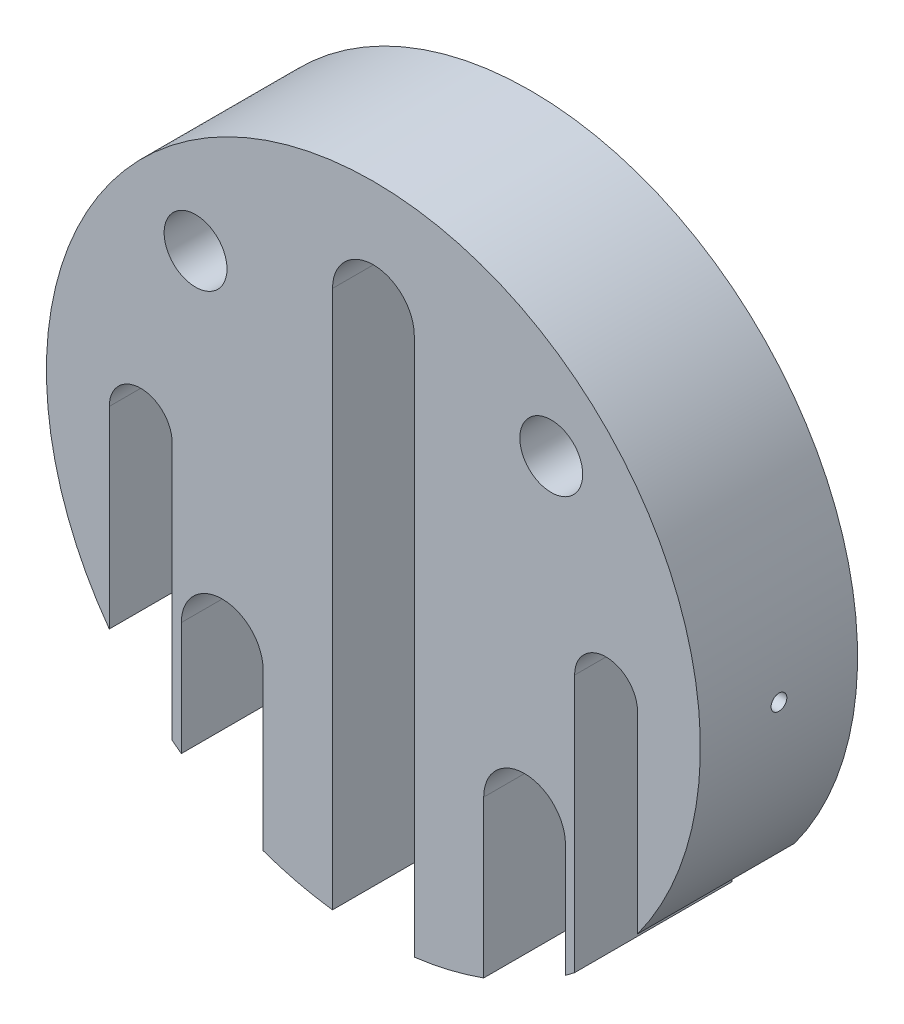
SolidWorks part; units mm, degrees
material "Malleable Cast Iron"
ref_plane "Front Plane" through (0, 0, 0) normal (0, 0, 1) x (1, 0, 0)
ref_plane "Top Plane" through (0, 0, 0) normal (0, 1, 0) x (1, 0, 0)
ref_plane "Right Plane" through (0, 0, 0) normal (1, 0, 0) x (0, 0, -1)
sketch "Sketch1" plane through (0, 0, 0) normal (0, 0, 1) x (1, 0, 0)
  circle A0 centre (0, 0) radius 52
  dimension "D1" = 104
extrude "Boss-Extrude1" add sketch "Sketch1" along normal blind 25
sketch "Sketch2" plane through (0, 0, 25) normal (0, 0, 1) x (1, 0, 0)
  line L0 (0, 0) -> (0, -16.5156) construction
  line L2 (32, 0) -> (32, -45)
  line L3 (32, -45) -> (42, -45)
  line L4 (42, 0) -> (42, -45)
  line L6 (-5, -40) -> (-5, -55)
  line L7 (-5, -55) -> (5, -55)
  line L8 (5, -40) -> (5, -55)
  line L9 (-32, -45) -> (-42, -45)
  line L10 (-42, 0) -> (-42, -45)
  line L12 (-32, 0) -> (-32, -45)
  arc A1 (32, 0) -> (42, 0) centre (37, 0) cw
  arc A2 (-32, 0) -> (-42, 0) centre (-37, 0) ccw
  arc A3 (5, -40) -> (-5, -40) centre (0, -40) ccw
  dimension "D9" = 5
  dimension "D3" = 5
  dimension "D2" = 5
extrude "Cut-Extrude1" cut sketch "Sketch2" against normal blind 25
sketch "Sketch3" plane through (0, 0, 25) normal (0, 0, 1) x (1, 0, 0)
  circle A0 centre (0, 34) radius 6.5
  dimension "D1" = 13
  dimension "D2" = 34
extrude "Cut-Extrude2" cut sketch "Sketch3" against normal blind 30 contours A0
sketch "Sketch5" plane through (0, 0, 25) normal (0, 0, 1) x (1, 0, 0)
  line L0 (0, 0) -> (-24.0416, -24.0416) construction
  line L1 (0, 0) -> (0, -28.0674) construction
  circle A0 centre (-24.0416, -24.0416) radius 6.5
  dimension "D1" = 13
  dimension "D2" = 34
  dimension "D3" = 45
extrude "Cut-Extrude3" cut sketch "Sketch5" against normal blind 30
mirror "Mirror1" about plane through (0, 0, 0) normal (1, 0, 0) of "Cut-Extrude3"
sketch "Sketch6" plane through (0, 0, 25) normal (0, 0, 1) x (1, 0, 0)
  line L0 (-6.5, 34) -> (6.5, 34)
  line L1 (-6.5, 34) -> (-6.5, -56.1062)
  line L2 (6.5, 34) -> (6.5, -56.1062)
  line L3 (-6.5, -56.1062) -> (6.5, -56.1062)
  line L4 (17.5416, -24.0416) -> (30.5416, -24.0416)
  line L5 (17.5416, -24.0416) -> (17.5416, -50.2523)
  line L6 (30.5416, -24.0416) -> (30.5416, -50.2523)
  line L7 (17.5416, -50.2523) -> (30.5416, -50.2523)
  line L8 (-30.5416, -24.0416) -> (-17.5416, -24.0416)
  line L9 (-30.5416, -24.0416) -> (-30.5416, -53.8028)
  line L10 (-17.5416, -24.0416) -> (-17.5416, -53.8028)
  line L11 (-30.5416, -53.8028) -> (-17.5416, -53.8028)
  circle A0 centre (0, 34) radius 6.5 construction
  circle A1 centre (24.0416, -24.0416) radius 6.5 construction
  circle A2 centre (-24.0416, -24.0416) radius 6.5 construction
extrude "Cut-Extrude4" cut sketch "Sketch6" against normal blind 30
ref_plane "Plane1" through (-52, 0, 0) normal (-1, 0, 0) x (0, 0, 1)
hole_wizard "M3 Tapped Hole1" positions "Sketch8" profile "Sketch9" tap size "M3" standard "ISO"
sketch "Sketch8" plane through (-52, 0, 0) normal (-1, 0, 0) x (0, 0, 1)
  line L0 (0, 52) -> (0, -30.6594) construction
  point P0 (12.5, 0)
  dimension "D1" = 12.5
sketch "Sketch9" plane through (-52, 0, 12.5) normal (0, 1, 0) x (0, 0, 1)
  line L0 (0, 0) -> (0, 45.5)
  line L1 (0, 45.5) -> (1.25, 45.5)
  line L2 (1.25, 45.5) -> (1.25, 0)
  line L5 (1.25, 0) -> (0, 0)
  line L11 (0, -6.35) -> (0, 107.95) construction
  dimension "Thru Tap Drill Dia." = 2.5
  dimension "Thru Tap Drill Depth" = 45.5
cosmetic thread "Hole Thread2" parameters "D2"=3
mirror "Mirror2" about plane through (0, 0, 0) normal (1, 0, 0) of "M3 Tapped Hole1"
sketch "Sketch10" plane through (0, 0, 25) normal (0, 0, 1) x (1, 0, 0)
  line L0 (0, 0) -> (28.2843, 28.2843) construction
  line L1 (0, 0) -> (0, 27.2314) construction
  circle A0 centre (28.2843, 28.2843) radius 5
  dimension "D1" = 10
  dimension "D2" = 45
  dimension "D3" = 40
extrude "Cut-Extrude5" cut sketch "Sketch10" against normal blind 30
mirror "Mirror3" about plane through (0, 0, 0) normal (1, 0, 0) of "Cut-Extrude5"
